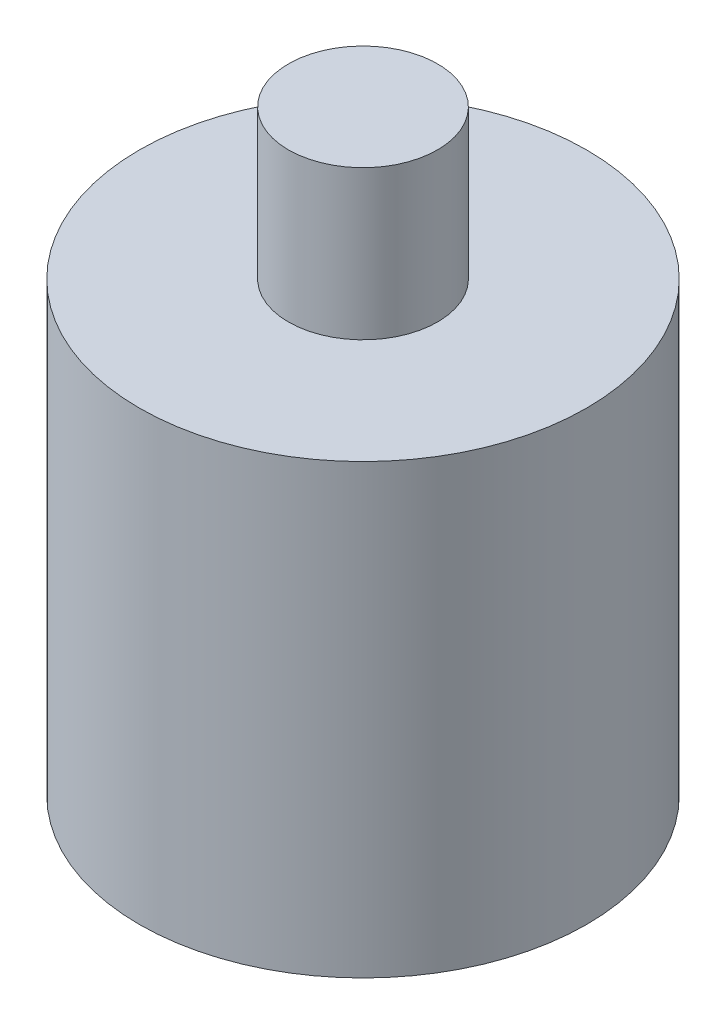
SolidWorks part; units mm, degrees
ref_plane "Front Plane" through (0, 0, 0) normal (0, 0, 1) x (1, 0, 0)
ref_plane "Top Plane" through (0, 0, 0) normal (0, 1, 0) x (1, 0, 0)
ref_plane "Right Plane" through (0, 0, 0) normal (1, 0, 0) x (0, 0, -1)
sketch "Sketch1" plane through (0, 0, 0) normal (0, 1, 0) x (1, 0, 0)
  circle A0 centre (0, 0) radius 15
  dimension "D1" = 30
extrude "Boss-Extrude1" add sketch "Sketch1" along normal blind 30
sketch "Sketch2" plane through (0, 30, 0) normal (0, 1, 0) x (1, 0, 0)
  circle A0 centre (0, 0) radius 5
  dimension "D1" = 10
extrude "Boss-Extrude2" add sketch "Sketch2" along normal blind 10
